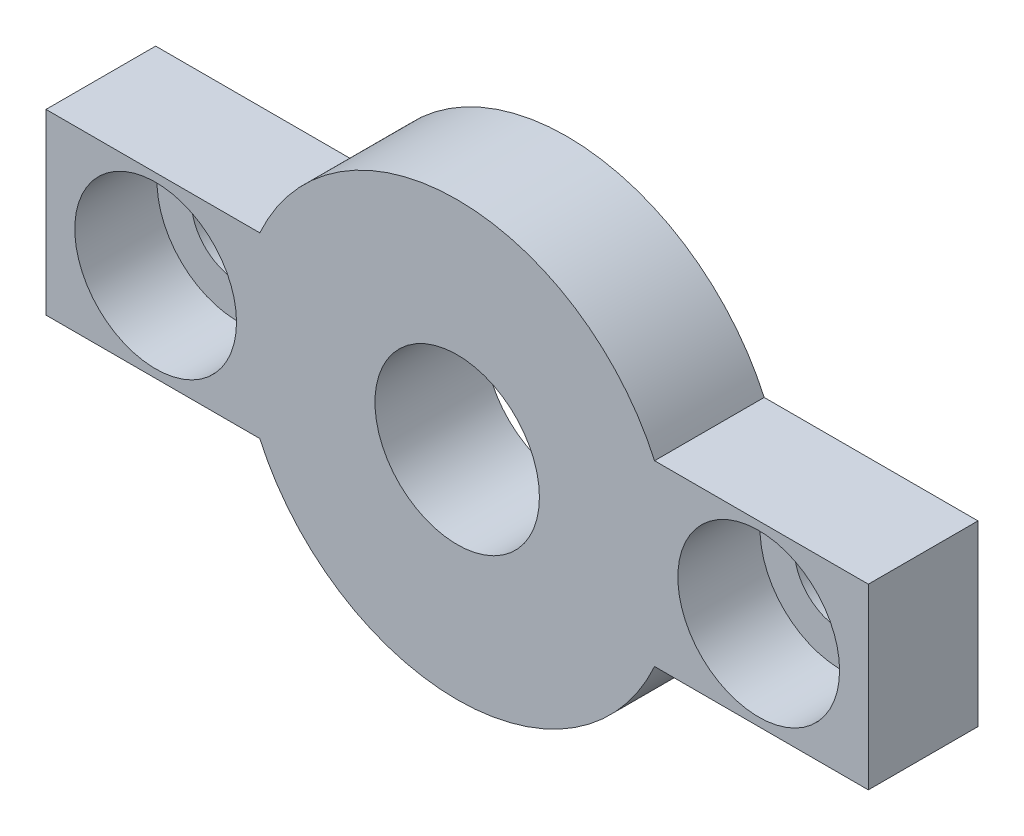
SolidWorks part; units mm, degrees
ref_plane "Alzado" through (0, 0, 0) normal (0, 0, 1) x (1, 0, 0)
ref_plane "Planta" through (0, 0, 0) normal (0, 1, 0) x (1, 0, 0)
ref_plane "Vista lateral" through (0, 0, 0) normal (1, 0, 0) x (0, 0, -1)
sketch "Croquis1" plane through (0, 0, 0) normal (0, 0, 1) x (1, 0, 0)
  line L0 (-7.2005, 3.25) -> (-15, 3.25)
  line L1 (15, -3.25) -> (7.2005, -3.25)
  line L2 (15, -3.25) -> (15, 3.25)
  line L3 (15, 3.25) -> (7.2005, 3.25)
  line L4 (-15, -3.25) -> (-15, 3.25)
  line L5 (15, -3.25) -> (-15, 3.25) construction
  line L6 (15, 3.25) -> (-15, -3.25) construction
  line L9 (-7.2005, -3.25) -> (-15, -3.25)
  arc A0 (-7.2005, -3.25) -> (7.2005, -3.25) centre (0, 0) ccw
  circle A1 centre (0, 0) radius 3
  arc A2 (7.2005, 3.25) -> (-7.2005, 3.25) centre (0, 0) ccw
  dimension "D3" = 6
  dimension "D4" = 7.9
  dimension "D1" = 30
  dimension "D2" = 6.5
extrude "Saliente-Extruir1" add sketch "Croquis1" along normal blind 4
sketch "Croquis2" plane through (0, 0, 4) normal (0, 0, 1) x (1, 0, 0)
  line L0 (-11, 0) -> (11, 0) construction
  circle A0 centre (-11, 0) radius 1.7
  circle A1 centre (11, 0) radius 1.7
  point P2 (0, 0)
  dimension "D1" = 3.4
  dimension "D2" = 22
extrude "Cortar-Extruir1" cut sketch "Croquis2" against normal blind 4
sketch "Croquis3" plane through (0, 0, 4) normal (0, 0, 1) x (1, 0, 0)
  circle A0 centre (-11, 0) radius 2.95
  circle A1 centre (11, 0) radius 2.95
  dimension "D1" = 5.9
extrude "Cortar-Extruir2" cut sketch "Croquis3" against normal blind 3
